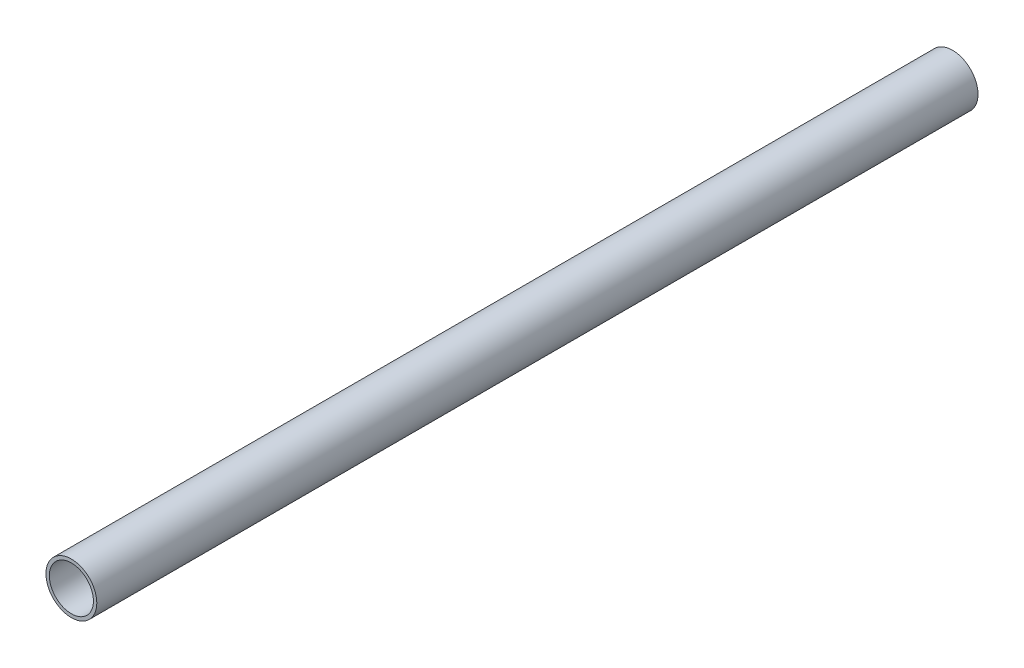
SolidWorks part; units mm, degrees
ref_plane "Front Plane" through (0, 0, 0) normal (0, 0, 1) x (1, 0, 0)
ref_plane "Top Plane" through (0, 0, 0) normal (0, 1, 0) x (1, 0, 0)
ref_plane "Right Plane" through (0, 0, 0) normal (1, 0, 0) x (0, 0, -1)
sketch "Sketch1" plane through (0, 0, 0) normal (0, 0, 1) x (1, 0, 0)
  circle A0 centre (0, 0) radius 9.525
  circle A1 centre (0, 0) radius 8.255
  dimension "D1" = 19.05
  dimension "D2" = 1.27
extrude "Boss-Extrude1" add sketch "Sketch1" along normal blind 330.2
